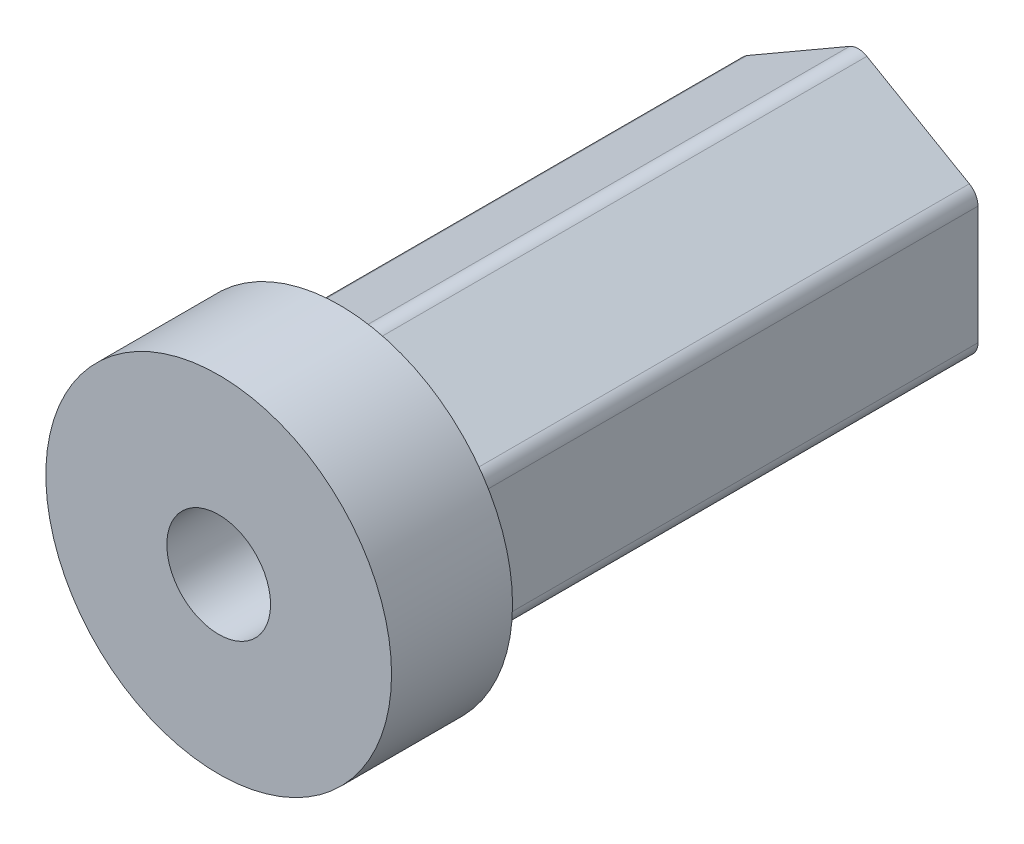
SolidWorks part; units mm, degrees
ref_plane "Front Plane" through (0, 0, 0) normal (0, 0, 1) x (1, 0, 0)
ref_plane "Top Plane" through (0, 0, 0) normal (0, 1, 0) x (1, 0, 0)
ref_plane "Right Plane" through (0, 0, 0) normal (1, 0, 0) x (0, 0, -1)
sketch "Sketch2" plane through (0, 0, 0) normal (1, 0, 0) x (0, 0, -1)
  line L0 (0, 0) -> (38.379, 0) construction
  line L1 (-12, 3) -> (25, 3)
  line L2 (25, 3) -> (25, 8)
  line L3 (25, 8) -> (-5, 8)
  line L4 (-5, 8) -> (-5, 10)
  line L5 (-5, 10) -> (-12, 10)
  line L6 (-12, 10) -> (-12, 3)
  dimension "D1" = 6
  dimension "D2" = 5
  dimension "D3" = 7
  dimension "D4" = 30
  dimension "D5" = 7
  dimension "D6" = 25
revolve "Revolve1" add sketch "Sketch2" angle 360 about L0
sketch "Sketch3" plane through (0, 0, -25) normal (0, 0, -1) x (-1, 0, 0)
  line L1 (0, -8) -> (6.9282, -4)
  line L2 (6.9282, -4) -> (6.9282, 4)
  line L3 (6.9282, 4) -> (0, 8)
  line L4 (0, 8) -> (-6.9282, 4)
  line L5 (-6.9282, 4) -> (-6.9282, -4)
  line L6 (-6.9282, -4) -> (0, -8)
  circle A0 centre (0, 0) radius 6.9282 construction
  circle A1 centre (0, 0) radius 8
  circle A2 centre (0, 0) radius 8 construction
  circle M1 centre (0, 0) radius 8
extrude "Cut-Extrude1" cut sketch "Sketch3" against normal blind 30 contours L4 M1 | L5 M1 | L6 M1 | L1 M1 | L2 M1 | L3 M1
fillet "Fillet1" radius 1 6 edges at (-6.9282, 4, -10) (-6.9282, -4, -10) (0, -8, -10) (6.9282, -4, -10) (6.9282, 4, -10) (0, 8, -10)
